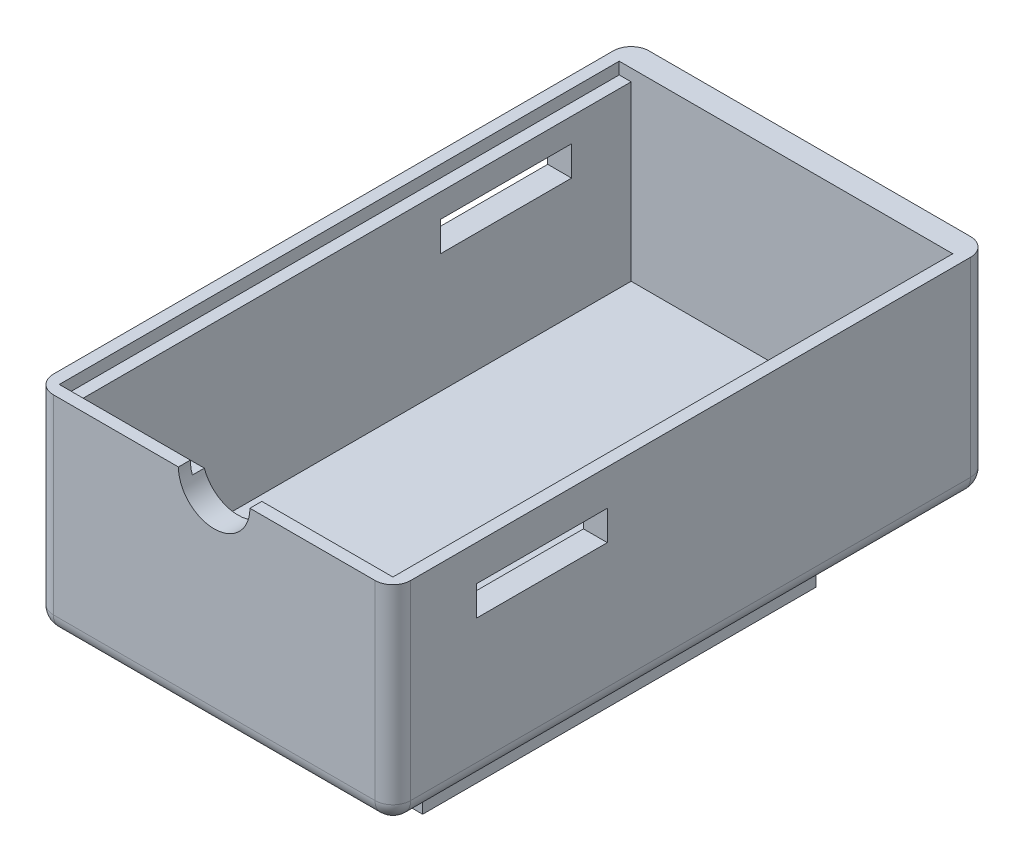
SolidWorks part; units mm, degrees
ref_plane "Front Plane" through (0, 0, 0) normal (0, 0, 1) x (1, 0, 0)
ref_plane "Top Plane" through (0, 0, 0) normal (0, 1, 0) x (1, 0, 0)
ref_plane "Right Plane" through (0, 0, 0) normal (1, 0, 0) x (0, 0, -1)
sketch "Sketch1" plane through (0, 0, 0) normal (0, 1, 0) x (1, 0, 0)
  line L1 (-15, 20) -> (15, 20)
  line L2 (-15, 20) -> (-15, -20)
  line L4 (15, 20) -> (15, -20)
  line L5 (-15, 20) -> (15, -20) construction
  line L6 (-15, -20) -> (15, 20) construction
  line L8 (-15, -20) -> (-15, -30)
  line L9 (-15, -30) -> (15, -30)
  line L10 (15, -20) -> (15, -30)
  point P0 (0, 0)
  dimension "D1" = 30
  dimension "D2" = 40
  dimension "D3" = 10
extrude "Boss-Extrude1" add sketch "Sketch1" along normal blind 17.5
shell "Shell1" thickness 2
fillet "Fillet1" radius 1.5 8 edges at (-15, 0, 5) (15, 0, 5) (0, 0, -20) (-15, 8.75, -20) (15, 8.75, -20) (0, 0, 30) (15, 8.75, 30) (-15, 8.75, 30)
sketch "Sketch7" plane through (13, 0, 0) normal (-1, 0, 0) x (0, 0, 1)
  line L3 (23, 14.5) -> (12, 14.5)
  line L8 (23, 14.5) -> (23, 12)
  line L9 (23, 12) -> (12, 12)
  line L10 (12, 14.5) -> (12, 12)
  dimension "D2" = 2.5
  dimension "D3" = 11
extrude "Cut-Extrude3" cut sketch "Sketch7" against normal up to next contours L3 L10 L9 L8
sketch "Sketch8" plane through (-13, 0, 0) normal (1, 0, 0) x (0, 0, -1)
  line L4 (13, 14.5) -> (2, 14.5)
  line L5 (13, 14.5) -> (13, 12)
  line L6 (13, 12) -> (2, 12)
  line L7 (2, 14.5) -> (2, 12)
  dimension "D3" = 2.5
  dimension "D4" = 11
extrude "Cut-Extrude4" cut sketch "Sketch8" against normal up to next
sketch "Sketch9" plane through (0, 17.5, 0) normal (0, 1, 0) x (1, 0, 0)
  line L0 (-13, 18) -> (-14, 18)
  line L6 (-14, 18) -> (-14, -19)
  line L8 (-13, 18) -> (-13, -18)
  line L10 (13, 18) -> (13, -18)
  line L12 (14, 18) -> (14, -19)
  line L13 (-13.2632, 18) -> (13, -17.6429) construction
  line L14 (-13, -17.6429) -> (13.2632, 18) construction
  line L15 (13, 18) -> (14, 18)
  line L18 (-14, -19) -> (-14, -29)
  line L25 (-13, -18) -> (-13, -28)
  line L26 (-13, 18) -> (-13, -28) construction
  line L27 (-13, -28) -> (13, -28)
  line L28 (13, -28) -> (13, -18)
  line L29 (14, -19) -> (14, -29)
  line L30 (14, -29) -> (-14, -29)
  point P0 (0, 0)
  point P1 (0, 0)
  point P6 (0, 0)
  dimension "D1" = 10
  dimension "D2" = 36
  dimension "D3" = 28
  dimension "D4" = 10
extrude "Cut-Extrude5" cut sketch "Sketch9" against normal blind 1
sketch "Sketch10" plane through (0, 0, 30) normal (0, 0, 1) x (1, 0, 0)
  line L0 (-13.5, 17.5) -> (13.5, 17.5) construction
  line L1 (-3, 17.5) -> (3, 17.5)
  arc A0 (-3, 17.5) -> (3, 17.5) centre (0, 17.5) ccw
  dimension "D1" = 6
extrude "Cut-Extrude6" cut sketch "Sketch10" against normal up to next
sketch "Sketch11" plane through (0, 0, 0) normal (0, -1, 0) x (1, 0, 0)
  line L0 (-7, 5.5244) -> (0, 5.5244)
  line L1 (-7, 19.5244) -> (0, 19.5244)
  line L2 (1, 5.5244) -> (7, 5.5244)
  line L3 (-7, 19.5244) -> (0, 19.5244)
  line L5 (-9, 21.5) -> (-9, -11.5)
  line L6 (-9, -11.5) -> (6.25, -11.5)
  line L8 (-7, 19.5244) -> (-7, 13.5244)
  line L11 (-7, 19.5244) -> (-7, 13.5244)
  line L13 (0, 19.5244) -> (0, 17.7244)
  line L14 (0, 17.7244) -> (1, 17.7244)
  line L15 (1, 19.5244) -> (1, 17.7244)
  line L16 (-7, 12.5244) -> (-7, 5.5244)
  line L17 (-7, 13.5244) -> (-4.2, 13.5244)
  line L19 (-7, 12.5244) -> (-4.2, 12.5244)
  line L20 (-4.2, 13.5244) -> (-4.2, 12.5244)
  line L22 (0, 5.5244) -> (0, 8.3244)
  line L23 (0, 8.3244) -> (1, 8.3244)
  line L24 (1, 5.5244) -> (1, 8.3244)
  line L25 (7, 5.5244) -> (7, 12.5244)
  line L26 (7, 12.5244) -> (5.2, 12.5244)
  line L27 (5.2, 12.5244) -> (5.2, 13.5244)
  line L28 (5.2, 13.5244) -> (7, 13.5244)
  line L29 (7, 13.5244) -> (7, 19.5244)
  line L30 (7, 19.5244) -> (6.25, 19.5244)
  line L31 (-9, 21.5) -> (7, 21.5)
  line L32 (7, 21.5) -> (9, 21.5)
  line L33 (9, 21.5) -> (9, -11.5)
  line L34 (9, -11.5) -> (6.25, -11.5)
  line L35 (1, 19.5244) -> (6.25, 19.5244)
  line L36 (-7, 12.5244) -> (-7, 5.5244)
  line L37 (13.5, 28.5) -> (-13.5, 28.5) construction
  line L38 (7.285, -9.5) -> (6.535, -9.5)
  line L39 (1.285, -9.5) -> (6.535, -9.5)
  line L40 (7.285, -3.5) -> (7.285, -9.5)
  line L41 (7.285, 4.5244) -> (7.285, -2.5)
  line L42 (1, 4.5244) -> (7.285, 4.5244)
  line L43 (-7, 4.5244) -> (0, 4.5244)
  line L44 (-7, -2.4756) -> (-7, 4.5244)
  line L46 (-6.715, -9.5) -> (0.285, -9.5)
  line L47 (0, 1.7244) -> (1, 1.7244)
  line L48 (0, 4.5244) -> (0, 1.7244)
  line L49 (1, 4.5244) -> (1, 1.7244)
  line L50 (7.285, -2.5) -> (5.485, -2.5)
  line L51 (5.485, -3.5) -> (7.285, -3.5)
  line L52 (5.485, -2.5) -> (5.485, -3.5)
  line L53 (-3.915, -3.5) -> (-3.915, -2.4756)
  line L54 (-7, -2.4756) -> (-3.915, -2.4756)
  line L55 (-6.715, -3.5) -> (-3.915, -3.5)
  line L56 (0.285, -7.7) -> (1.285, -7.7)
  line L57 (1.285, -9.5) -> (1.285, -7.7)
  line L58 (0.285, -9.5) -> (0.285, -7.7)
  line L59 (-13.5, -18.5) -> (13.5, -18.5) construction
  line L60 (13.5, -18.5) -> (13.5, 28.5) construction
  line L61 (-13.5, 28.5) -> (-13.5, -18.5) construction
  line L62 (-7, -3.5) -> (-7, -9.5)
  line L63 (-7, -9.5) -> (-6.715, -9.5)
  line L64 (-7, -3.5) -> (-6.715, -3.5)
  point P0 (-0.09, 4.8994)
  point P6 (-0.09, 4.8994)
  dimension "D2" = 2
  dimension "D3" = 2
  dimension "D4" = 14
  dimension "D5" = 7
  dimension "D6" = 1
  dimension "D7" = 1.8
  dimension "D8" = 6
  dimension "D9" = 1
  dimension "D10" = 2.8
  dimension "D11" = 7
  dimension "D12" = 1
  dimension "D13" = 2.8
  dimension "D14" = 6
  dimension "D15" = 1.8
  dimension "D16" = 1
  dimension "D17" = 2
  dimension "D18" = 7
  dimension "D19" = 15.25
  dimension "D20" = 7
  dimension "D21" = 4.5
  dimension "D22" = 4.5
  dimension "D23" = 1.8
extrude "Boss-Extrude2" add sketch "Sketch11" along normal blind 6 contours L34 L33 L32 L31 L5 L6 L15 L35 L30 L29 L28 L27 L26 L25 L2 L24 L23 L22 L0 L16 L19 L20 L17 L8 L1 L13 L14 L62 L64 L55 L53 L54 L44 L43 L48 L47 L49 L42 L41 L50 L52 L51 L40 L38 L39 L57 L56 L58 L46
fillet "Fillet2" radius 2 4 edges at (-9, 0, 5) (0, 0, 21.5) (0, 0, -11.5) (9, 0, 5)
fillet "Fillet3" radius 1 8 edges at (5.2, -6, 13.0244) (0.5, -6, 17.7244) (-4.2, -6, 13.0244) (0.5, -6, 8.3244) (5.485, -6, -3) (0.785, -6, -7.7) (-3.915, -6, -2.9878) (0.5, -6, 1.7244)
